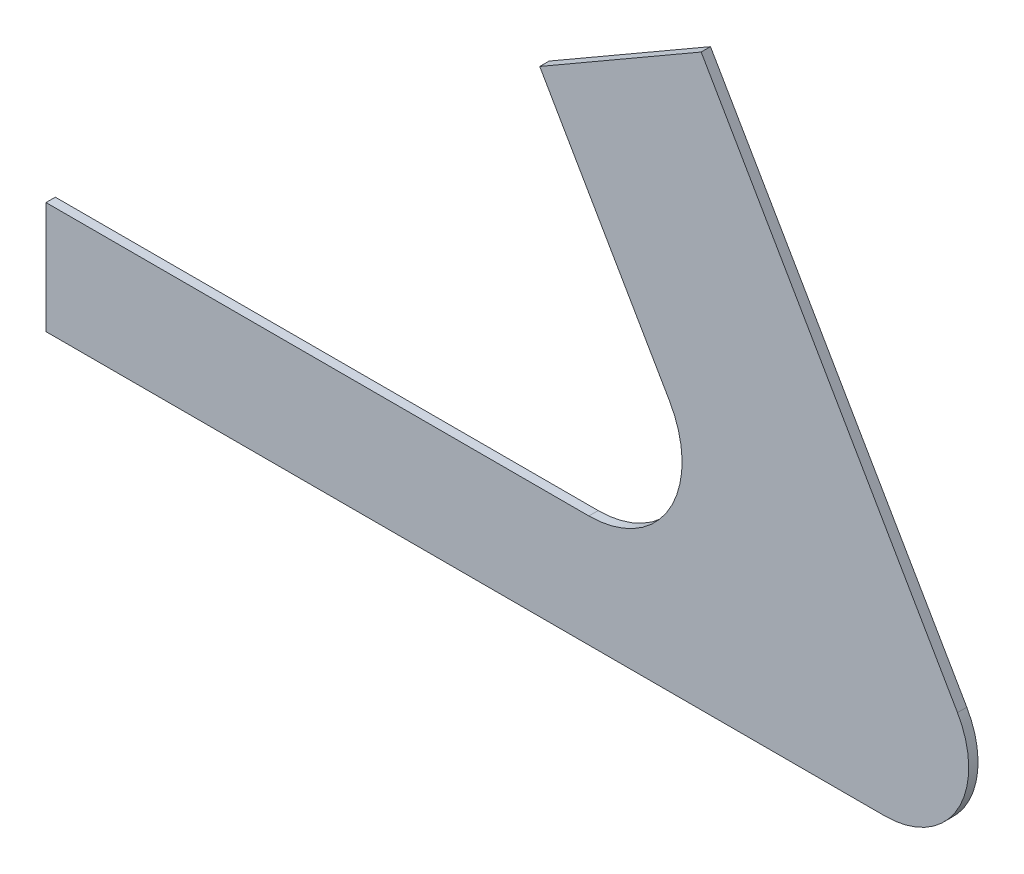
SolidWorks part; units mm, degrees
ref_plane "Płaszczyzna przednia" through (0, 0, 0) normal (0, 0, 1) x (1, 0, 0)
ref_plane "Płaszczyzna górna" through (0, 0, 0) normal (0, 1, 0) x (1, 0, 0)
ref_plane "Płaszczyzna prawa" through (0, 0, 0) normal (1, 0, 0) x (0, 0, -1)
sketch "Szkic1" plane through (0, 0, 0) normal (0, 0, 1) x (1, 0, 0)
  line L0 (0, 0) -> (0, 12)
  line L1 (70.2942, 61.1314) -> (52.9737, 51.1314)
  line L2 (97.7942, 13.5) -> (70.2942, 61.1314)
  line L3 (52.9737, 51.1314) -> (66.906, 27)
  line L4 (0, 12) -> (58.2457, 12)
  line L5 (90, 0) -> (0, 0)
  line L6 (55, 0) -> (-55, 0) construction
  arc A0 (66.906, 27) -> (58.2457, 12) centre (58.2457, 22) cw
  arc A1 (90, 0) -> (97.7942, 13.5) centre (90, 9) ccw
  point P11 (0, 0)
  dimension "D3" = 10
  dimension "D6" = 9
  dimension "D1" = 12
  dimension "D2" = 20
  dimension "D5" = 55
  dimension "D7" = 60
  dimension "D8" = 90
  dimension "D9" = 58.2457
extrude "Dodanie-wyciągnięcie1" add sketch "Szkic1" along normal blind 1
